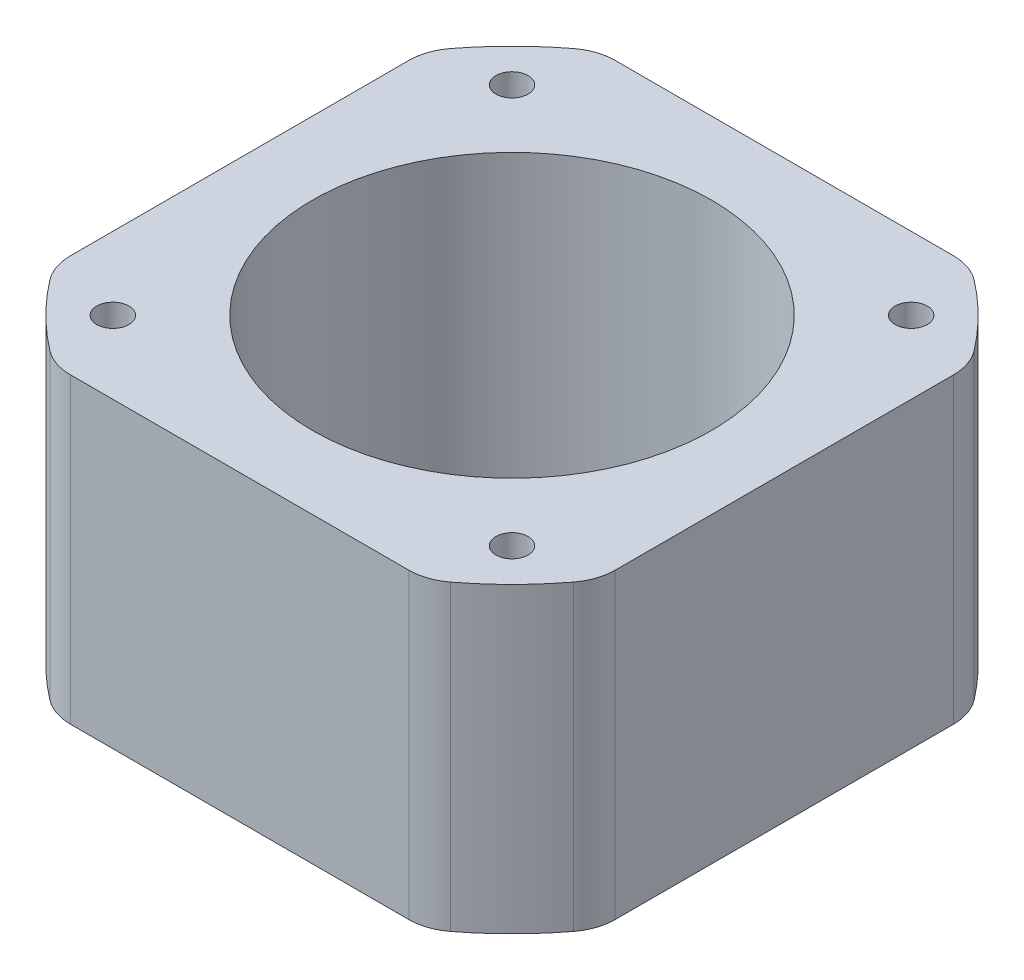
SolidWorks part; units mm, degrees
ref_plane "Спереди" through (0, 0, 0) normal (0, 0, 1) x (1, 0, 0)
ref_plane "Сверху" through (0, 0, 0) normal (0, 1, 0) x (1, 0, 0)
ref_plane "Справа" through (0, 0, 0) normal (1, 0, 0) x (0, 0, -1)
sketch "Эскиз1" plane through (0, 0, 0) normal (0, 1, 0) x (1, 0, 0)
  line L1 (-14.4235, -21.15) -> (14.4235, -21.15)
  line L2 (-21.15, -14.4235) -> (-21.15, 14.4235)
  line L3 (-14.4235, 21.15) -> (14.4235, 21.15)
  line L4 (21.15, -14.4235) -> (21.15, 14.4235)
  line L5 (-21.15, -21.15) -> (21.15, 21.15) construction
  line L6 (-21.15, 21.15) -> (21.15, -21.15) construction
  line L10 (-15.5, -15.5) -> (15.5, -15.5) construction
  line L11 (-15.5, -15.5) -> (-15.5, 15.5) construction
  line L12 (-15.5, 15.5) -> (15.5, 15.5) construction
  line L13 (15.5, -15.5) -> (15.5, 15.5) construction
  line L14 (-15.5, -15.5) -> (15.5, 15.5) construction
  line L15 (-15.5, 15.5) -> (15.5, -15.5) construction
  circle A0 centre (-15.5, 15.5) radius 1.25
  circle A1 centre (15.5, 15.5) radius 1.25
  circle A2 centre (15.5, -15.5) radius 1.25
  circle A3 centre (-15.5, -15.5) radius 1.25
  circle A4 centre (0, 0) radius 15.5
  arc A7 (-21.15, -14.4235) -> (-14.4235, -21.15) centre (0, 0) ccw
  arc A8 (-14.4235, 21.15) -> (-21.15, 14.4235) centre (0, 0) ccw
  arc A9 (21.15, 14.4235) -> (14.4235, 21.15) centre (0, 0) ccw
  arc A10 (14.4235, -21.15) -> (21.15, -14.4235) centre (0, 0) ccw
  point P0 (0, 0)
  point P13 (0, 0)
  dimension "D9" = 2.5
  dimension "D14" = 25.6
  dimension "D15" = 31
  dimension "D16" = 42.3
extrude "Бобышка-Вытянуть1" add sketch "Эскиз1" along normal blind 23.5
fillet "Скругление1" radius 4 8 edges at (-21.15, 11.75, -14.4235) (-14.4235, 11.75, -21.15) (14.4235, 11.75, -21.15) (21.15, 11.75, -14.4235) (21.15, 11.75, 14.4235) (14.4235, 11.75, 21.15) (-14.4235, 11.75, 21.15) (-21.15, 11.75, 14.4235)
